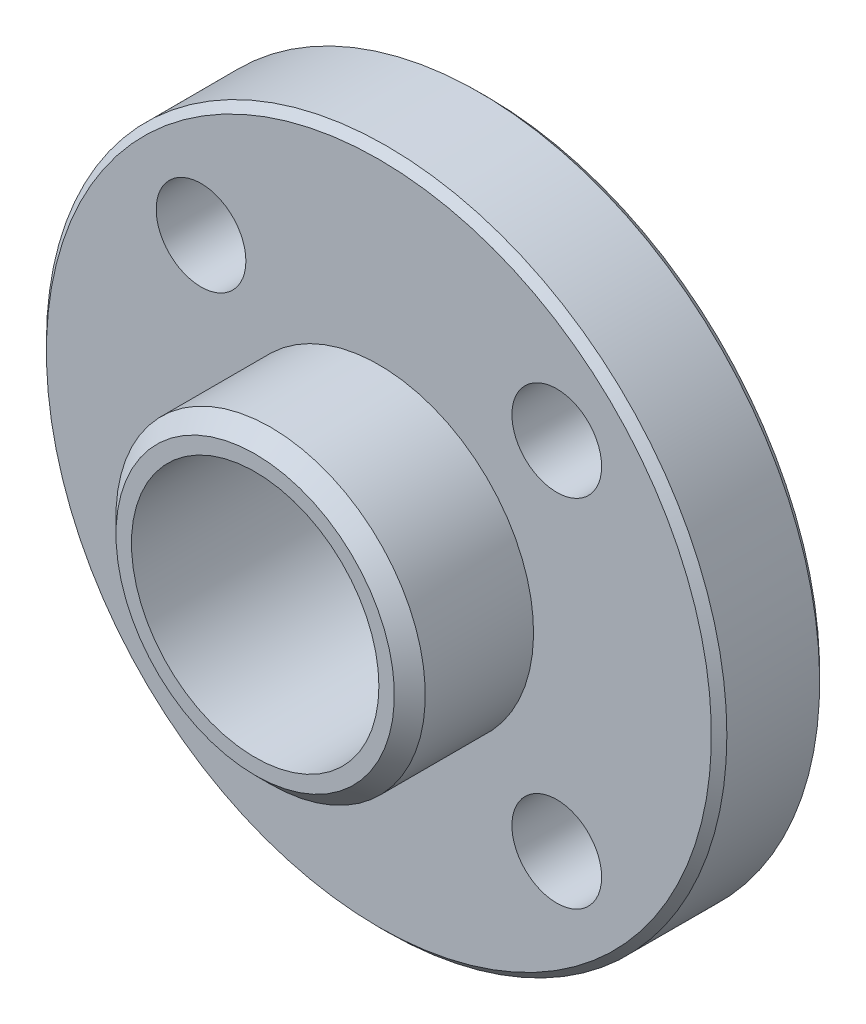
SolidWorks part; units mm, degrees
material "Brass"
ref_plane "Front Plane" through (0, 0, 0) normal (0, 0, 1) x (1, 0, 0)
ref_plane "Top Plane" through (0, 0, 0) normal (0, 1, 0) x (1, 0, 0)
ref_plane "Right Plane" through (0, 0, 0) normal (1, 0, 0) x (0, 0, -1)
sketch "Sketch1" plane through (0, 0, 0) normal (1, 0, 0) x (0, 0, -1)
  line L0 (-5.75, 0) -> (-5.75, 5)
  line L1 (-5.75, 5) -> (-1.75, 5)
  line L2 (-1.75, 5) -> (-1.75, 11)
  line L3 (-1.75, 11) -> (1.75, 11)
  line L4 (1.75, 11) -> (1.75, 5)
  line L5 (1.75, 5) -> (5.75, 5)
  line L6 (5.75, 5) -> (5.75, 0)
  line L7 (-5.75, 0) -> (5.75, 0) construction
  line L8 (-5.75, 0) -> (5.75, 0)
  point P2 (0, 11)
  point P11 (0, 0)
  dimension "D1" = 11
  dimension "D2" = 5
  dimension "D3" = 11.5
  dimension "D4" = 4
  dimension "D5" = 4
revolve "Revolve1" add sketch "Sketch1" angle 360 about L7
sketch "Sketch2" plane through (0, 0, 5.75) normal (0, 0, 1) x (1, 0, 0)
  circle A0 centre (0, 0) radius 4
  dimension "D1" = 8
extrude "Cut-Extrude1" cut sketch "Sketch2" against normal through all
chamfer "Chamfer1" distance 0.5 angle 45 2 edges at (0, -5, -5.75) (0, -5, 5.75)
chamfer "Chamfer2" distance 0.25 angle 45 2 edges at (0, -11, 1.75) (0, -11, -1.75)
hole_wizard "M3.5x0.6 Tapped Hole1" positions "Sketch3" profile "Sketch4" tap size "M3.5x0.6" standard "ANSI Metric" end condition through all
sketch "Sketch3" plane through (0, 0, 1.75) normal (0, 0, 1) x (1, 0, 0)
  line L0 (-5.75, 5.75) -> (-5.75, -5.75) construction
  line L1 (-5.75, -5.75) -> (5.75, -5.75) construction
  line L2 (5.75, -5.75) -> (5.75, 5.75) construction
  line L3 (5.75, 5.75) -> (-5.75, 5.75) construction
  line L5 (-5.75, 5.75) -> (5.75, -5.75) construction
  point P0 (-5.75, 5.75)
  point P2 (5.75, 5.75)
  point P4 (5.75, -5.75)
  point P6 (-5.75, -5.75)
  point P23 (0, 0)
  dimension "D1" = 11.5
sketch "Sketch4" plane through (-5.75, 5.75, 1.75) normal (1, 0, 0) x (0, -1, 0)
  line L0 (0, 0) -> (0, 7.5)
  line L1 (0, 7.5) -> (1.45, 7.5)
  line L2 (1.45, 7.5) -> (1.45, 0)
  line L5 (1.45, 0) -> (0, 0)
  line L11 (0, -6.35) -> (0, 107.95) construction
  dimension "Thru Tap Drill Dia." = 2.9
  dimension "Thru Tap Drill Depth" = 7.5
cosmetic thread "Hole Thread1" parameters "D2"=3.5
cosmetic thread "Hole Thread2" parameters "D2"=3.5
cosmetic thread "Hole Thread3" parameters "D2"=3.5
cosmetic thread "Hole Thread4" parameters "D2"=3.5
